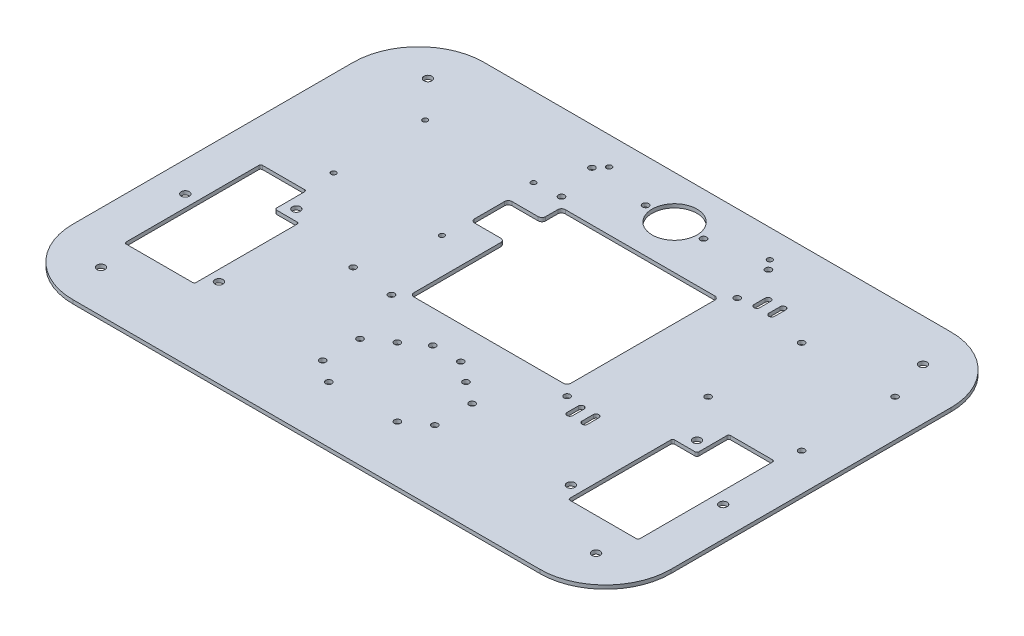
SolidWorks part; units mm, degrees
ref_plane "Front Plane" through (0, 0, 0) normal (0, 0, 1) x (1, 0, 0)
ref_plane "Top Plane" through (0, 0, 0) normal (0, 1, 0) x (1, 0, 0)
ref_plane "Right Plane" through (0, 0, 0) normal (1, 0, 0) x (0, 0, -1)
sketch "Sketch1" plane through (0, 0, 0) normal (0, 1, 0) x (1, 0, 0)
  line L0 (0, 110) -> (0, 0) construction
  line L5 (125, -110) -> (-125, -110)
  line L6 (160, -75) -> (160, 75)
  line L7 (125, 110) -> (-125, 110)
  line L8 (-160, -75) -> (-160, 75)
  line L9 (0, 0) -> (160, 0) construction
  arc A4 (125, 110) -> (160, 75) centre (125, 75) cw
  arc A5 (160, -75) -> (125, -110) centre (125, -75) cw
  arc A6 (-125, -110) -> (-160, -75) centre (-125, -75) cw
  arc A7 (-160, 75) -> (-125, 110) centre (-125, 75) cw
  point P0 (0, 0)
  dimension "D3" = 220
  dimension "D1" = 35
  dimension "D2" = 320
ref_plane "Plane1" through (0, -40, 0) normal (0, 1, 0) x (1, 0, 0)
sketch "Sketch2" plane through (0, 0, 0) normal (0, 1, 0) x (1, 0, 0)
  line L0 (100, -70) -> (100, -14)
  line L1 (100, -14) -> (113, -14)
  line L2 (113, -14) -> (113, 3)
  line L3 (113, 3) -> (137.5, 3)
  line L4 (137.5, 3) -> (137.5, -70)
  line L5 (137.5, -70) -> (100, -70)
  dimension "D1" = 37.5
  dimension "D2" = 73
  dimension "D3" = 13
  dimension "D4" = 56
  dimension "D5" = 100
  dimension "D6" = 70
sketch "Sketch3" plane through (0, 0, 0) normal (0, 1, 0) x (1, 0, 0)
  line L2 (113, -14) -> (113, 3) construction
  line L3 (100, -14) -> (113, -14) construction
  circle A0 centre (94.2, -62.6702) radius 2.15
  circle A1 centre (107.2, -8.2) radius 2.15
  circle A2 centre (143.9358, -30.9314) radius 2.15
  dimension "D1" = 4.3
  dimension "D4" = 59
  dimension "D5" = 13
  dimension "D7" = 5.8
  dimension "D6" = 5.8
  dimension "D2" = 56
  dimension "D3" = 43.2
sketch "Sketch4" plane through (0, 0, 0) normal (0, 1, 0) x (1, 0, 0)
  line L0 (0, 0) -> (0, 87) construction
  line L1 (0, 87) -> (15.5, 87) construction
  line L2 (0, 87) -> (-15.5, 87) construction
  circle A0 centre (0, 87) radius 12
  circle A1 centre (-15.5, 87) radius 1.65
  circle A2 centre (15.5, 87) radius 1.65
  dimension "D1" = 24
  dimension "D3" = 31
  dimension "D4" = 3.3
  dimension "D2" = 87
sketch "Sketch8" plane through (0, 0, 0) normal (0, 1, 0) x (1, 0, 0)
  line L1 (-132.5, -87.5) -> (132.5, -87.5) construction
  line L2 (-132.5, -87.5) -> (-132.5, 87.5) construction
  line L3 (-132.5, 87.5) -> (132.5, 87.5) construction
  line L4 (132.5, -87.5) -> (132.5, 87.5) construction
  line L5 (-132.5, -87.5) -> (132.5, 87.5) construction
  line L6 (-132.5, 87.5) -> (132.5, -87.5) construction
  circle A0 centre (-132.5, 87.5) radius 2.15
  circle A1 centre (132.5, 87.5) radius 2.15
  circle A2 centre (-132.5, -87.5) radius 2.15
  circle A3 centre (132.5, -87.5) radius 2.15
  point P0 (0, 0)
  dimension "D1" = 4.3
  dimension "D2" = 265
  dimension "D3" = 175
extrude "Boss-Extrude1" add sketch "Sketch1" against normal blind 2
extrude "Cut-Extrude8" cut sketch "Sketch2" against normal through all
extrude "Cut-Extrude9" cut sketch "Sketch3" against normal through all
extrude "Cut-Extrude10" cut sketch "Sketch4" against normal through all
extrude "Cut-Extrude11" cut sketch "Sketch8" against normal through all
fillet "Fillet1" radius 1 6 edges at (100, -1, 70) (137.5, -1, 70) (137.5, -1, -3) (100, -1, 14) (113, -1, 14) (113, -1, -3)
mirror "Mirror1" about plane through (0, 0, 0) normal (1, 0, 0) of "Fillet1", "Cut-Extrude8", "Cut-Extrude9"
sketch "Sketch10" plane through (0, 0, 0) normal (0, 1, 0) x (1, 0, 0)
  line L0 (0, 0) -> (0, -43) construction
  line L1 (18.35, -79.7) -> (-18.35, -79.7) construction
  line L2 (18.35, -79.7) -> (18.35, -43) construction
  line L3 (18.35, -43) -> (-18.35, -43) construction
  line L4 (-18.35, -79.7) -> (-18.35, -43) construction
  line L5 (18.35, -79.7) -> (-18.35, -43) construction
  line L6 (18.35, -43) -> (-18.35, -79.7) construction
  line L11 (-7.5, -34.9314) -> (0, -34.9314) construction
  line L13 (0, -34.9314) -> (7.5, -34.9314) construction
  line L14 (-114, 18.5) -> (-56, 18.5) construction
  line L15 (-114, 18.5) -> (-114, 67.5) construction
  line L16 (-114, 67.5) -> (-56, 67.5) construction
  line L17 (-56, 18.5) -> (-56, 67.5) construction
  line L18 (-114, 18.5) -> (-56, 67.5) construction
  line L19 (-114, 67.5) -> (-56, 18.5) construction
  line L20 (-143.9358, -30.9314) -> (143.9358, -30.9314) construction
  line L21 (-24, 23) -> (34, 23) construction
  line L24 (-35, -15.5) -> (45, -15.5) construction
  line L25 (-35, -15.5) -> (-35, 61.5) construction
  line L26 (-35, 61.5) -> (45, 61.5) construction
  line L27 (45, -15.5) -> (45, 61.5) construction
  line L28 (-35, -15.5) -> (45, 61.5) construction
  line L29 (-35, 61.5) -> (45, -15.5) construction
  line L30 (5, 23) -> (5, -15.5) construction
  line L31 (-35, 43) -> (-56, 43) construction
  line L32 (-55, 33) -> (-15, 33)
  line L33 (-55, 33) -> (-55, 53)
  line L34 (-55, 53) -> (-15, 53)
  line L35 (-15, 33) -> (-15, 53)
  line L36 (-55, 33) -> (-15, 53) construction
  line L37 (-55, 53) -> (-15, 33) construction
  circle A0 centre (18.35, -43) radius 1.65
  circle A1 centre (-18.35, -43) radius 1.65
  circle A2 centre (-18.35, -79.7) radius 1.65
  circle A3 centre (18.35, -79.7) radius 1.65
  circle A4 centre (-56, 67.5) radius 1.35
  circle A5 centre (-114, 67.5) radius 1.35
  circle A6 centre (-114, 18.5) radius 1.35
  circle A7 centre (-56, 18.5) radius 1.35
  circle A8 centre (-7.5, -34.9314) radius 1.65
  circle A9 centre (7.5, -34.9314) radius 1.65
  circle A11 centre (-24, 23) radius 1.35 construction
  circle A12 centre (34, 23) radius 1.35 construction
  circle A13 centre (0, 87) radius 22.2 construction
  point P0 (-85, 43)
  point P45 (-35, 43)
  dimension "D4" = 3.3
  dimension "D5" = 2.7
  dimension "D10" = 3.3
  dimension "D13" = 2.7
  dimension "D16" = 5
  dimension "D6" = 44.4
  dimension "D1" = 58
  dimension "D2" = 36.7
  dimension "D3" = 43
  dimension "D7" = 43
  dimension "D8" = 49
  dimension "D9" = 15
  dimension "D11" = 4
  dimension "D12" = 58
  dimension "D14" = 77
  dimension "D15" = 80
  dimension "D17" = 85
  dimension "D18" = 20
  dimension "D19" = 1
  dimension "D20" = 40
  dimension "D21" = 23
extrude "Cut-Extrude13" cut sketch "Sketch10" against normal through all
sketch "Sketch12" plane through (0, 0, 0) normal (0, 1, 0) x (1, 0, 0)
  line L5 (52, -22.5) -> (-42, -22.5) construction
  line L6 (52, -22.5) -> (52, 68.5) construction
  line L7 (52, 68.5) -> (-42, 68.5) construction
  line L8 (-37, -17.5) -> (47, -17.5)
  line L9 (47, -17.5) -> (47, 63.5)
  line L10 (-37, 63.5) -> (-37, -17.5)
  line L11 (47, 63.5) -> (-37, 63.5)
  line L12 (-37, -17.5) -> (47, -17.5)
  line L13 (47, -17.5) -> (47, 63.5)
  line L14 (-37, 63.5) -> (-37, -17.5)
  line L15 (47, 63.5) -> (-37, 63.5)
  line L16 (-42, -22.5) -> (-42, 68.5) construction
  line L17 (52, -22.5) -> (-42, 68.5) construction
  line L18 (52, 68.5) -> (-42, -22.5) construction
  circle A0 centre (-42, 68.5) radius 1.65
  circle A1 centre (52, 68.5) radius 1.65
  circle A2 centre (-42, -22.5) radius 1.65
  circle A3 centre (52, -22.5) radius 1.65
  point P0 (5, 23)
  dimension "D2" = 3.3
  dimension "D3" = 5
  dimension "D4" = 5
  dimension "D5" = 94
  dimension "D6" = 91
  dimension "D1" = 2
extrude "Cut-Extrude15" cut sketch "Sketch12" against normal through all
fillet "Fillet3" radius 2 8 edges at (47, -1, 17.5) (47, -1, -63.5) (-37, -1, 17.5) (-37, -1, -33) (-55, -1, -33) (-55, -1, -53) (-37, -1, -53) (-37, -1, -63.5)
sketch "Sketch11" plane through (0, 0, 0) normal (0, 1, 0) x (1, 0, 0)
  line L0 (-65, -20) -> (0, -20) construction
  line L1 (0, -20) -> (0, 0) construction
  line L2 (0, -20) -> (65, -20) construction
  line L4 (90, 15) -> (140, 15) construction
  line L5 (90, 15) -> (90, 65) construction
  line L6 (90, 65) -> (140, 65) construction
  line L7 (140, 15) -> (140, 65) construction
  line L8 (90, 15) -> (140, 65) construction
  line L9 (90, 65) -> (140, 15) construction
  circle A0 centre (90, 65) radius 1.65
  circle A1 centre (140, 65) radius 1.65
  circle A2 centre (90, 15) radius 1.65
  circle A3 centre (140, 15) radius 1.65
  circle A4 centre (65, -20) radius 1.65 construction
  circle A5 centre (-65, -20) radius 1.65
  point P2 (115, 40)
  dimension "D7" = 3.3
  dimension "D8" = 3.3
  dimension "D1" = 20
  dimension "D2" = 130
  dimension "D3" = 115
  dimension "D4" = 40
  dimension "D5" = 50
  dimension "D6" = 50
extrude "Cut-Extrude14" cut sketch "Sketch11" against normal through all
sketch "Sketch13" plane through (0, 0, 0) normal (0, 1, 0) x (1, 0, 0)
  line L0 (0, 110) -> (0, 95) construction
  line L1 (125, 110) -> (-125, 110) construction
  line L2 (-43, 95) -> (0, 95) construction
  line L3 (43, 95) -> (0, 95) construction
  line L4 (0, 95) -> (0, 90) construction
  line L5 (0, 90) -> (47.25, 90) construction
  line L6 (0, 90) -> (-47.25, 90) construction
  circle A0 centre (-47.25, 90) radius 1.65
  circle A1 centre (47.25, 90) radius 1.65
  circle A2 centre (-43, 95) radius 1.4
  circle A3 centre (43, 95) radius 1.4
  dimension "D3" = 2.8
  dimension "D4" = 3.3
  dimension "D6" = 6.5622
  dimension "D1" = 86
  dimension "D2" = 94.5
  dimension "D5" = 5
  dimension "D7" = 15
extrude "Cut-Extrude16" cut sketch "Sketch13" against normal through all
sketch "Sketch14" plane through (0, 0, 0) normal (0, 1, 0) x (1, 0, 0)
  line L0 (0, 0) -> (0, -55) construction
  line L1 (0, -55) -> (50, -55) construction
  line L2 (50, -55) -> (50, -51) construction
  line L3 (50, -55) -> (50, -59) construction
  line L4 (47, -51) -> (53, -51) construction
  line L5 (47, -49.5) -> (53, -49.5) construction
  line L6 (47, -52.5) -> (53, -52.5) construction
  line L7 (47, -59) -> (53, -59) construction
  line L8 (47, -57.5) -> (53, -57.5) construction
  line L9 (47, -60.5) -> (53, -60.5) construction
  line L10 (18.35, -43) -> (18.35, -79.7) construction
  line L11 (18.35, -61.35) -> (30, -61.35) construction
  line L12 (30, -61.35) -> (30, -51.35) construction
  line L13 (30, -61.35) -> (30, -71.35) construction
  arc A0 (47, -49.5) -> (47, -52.5) centre (47, -51) ccw construction
  arc A1 (53, -52.5) -> (53, -49.5) centre (53, -51) ccw construction
  arc A2 (47, -57.5) -> (47, -60.5) centre (47, -59) ccw construction
  arc A3 (53, -60.5) -> (53, -57.5) centre (53, -59) ccw construction
  circle A4 centre (30, -51.35) radius 1.65
  circle A5 centre (30, -71.35) radius 1.65
  point P8 (50, -51)
  point P14 (50, -59)
  dimension "D2" = 1.5
  dimension "D8" = 3.3
  dimension "D1" = 8
  dimension "D3" = 6
  dimension "D4" = 100
  dimension "D5" = 55
  dimension "D6" = 30
  dimension "D7" = 20
extrude "Cut-Extrude17" cut sketch "Sketch14" against normal through all
mirror "Mirror2" about plane through (0, 0, 0) normal (1, 0, 0) of "Cut-Extrude17"
sketch "Sketch16" plane through (0, 0, 0) normal (0, 1, 0) x (1, 0, 0)
  line L0 (61, 70) -> (61, 76) construction
  line L1 (59.5, 70) -> (59.5, 76)
  line L2 (62.5, 70) -> (62.5, 76)
  line L3 (69, 70) -> (69, 76) construction
  line L4 (67.5, 70) -> (67.5, 76)
  line L5 (70.5, 70) -> (70.5, 76)
  line L6 (61, -30) -> (61, -24) construction
  line L7 (59.5, -30) -> (59.5, -24)
  line L8 (62.5, -30) -> (62.5, -24)
  line L9 (69, -30) -> (69, -24) construction
  line L10 (67.5, -30) -> (67.5, -24)
  line L11 (70.5, -30) -> (70.5, -24)
  line L12 (61, 73) -> (69, 73) construction
  line L13 (61, -27) -> (69, -27) construction
  line L14 (65, 73) -> (65, -27) construction
  line L15 (65, 23) -> (47, 23) construction
  line L16 (47, -15.5) -> (47, 61.5) construction
  arc A0 (59.5, 70) -> (62.5, 70) centre (61, 70) ccw
  arc A1 (62.5, 76) -> (59.5, 76) centre (61, 76) ccw
  arc A2 (67.5, 70) -> (70.5, 70) centre (69, 70) ccw
  arc A3 (70.5, 76) -> (67.5, 76) centre (69, 76) ccw
  arc A4 (59.5, -30) -> (62.5, -30) centre (61, -30) ccw
  arc A5 (62.5, -24) -> (59.5, -24) centre (61, -24) ccw
  arc A6 (67.5, -30) -> (70.5, -30) centre (69, -30) ccw
  arc A7 (70.5, -24) -> (67.5, -24) centre (69, -24) ccw
  point P2 (61, 73)
  point P8 (69, 73)
  point P15 (61, -27)
  point P22 (69, -27)
  dimension "D2" = 1.5
  dimension "D3" = 100
  dimension "D1" = 6
  dimension "D4" = 8
  dimension "D5" = 18
extrude "Cut-Extrude18" cut sketch "Sketch16" against normal through all
